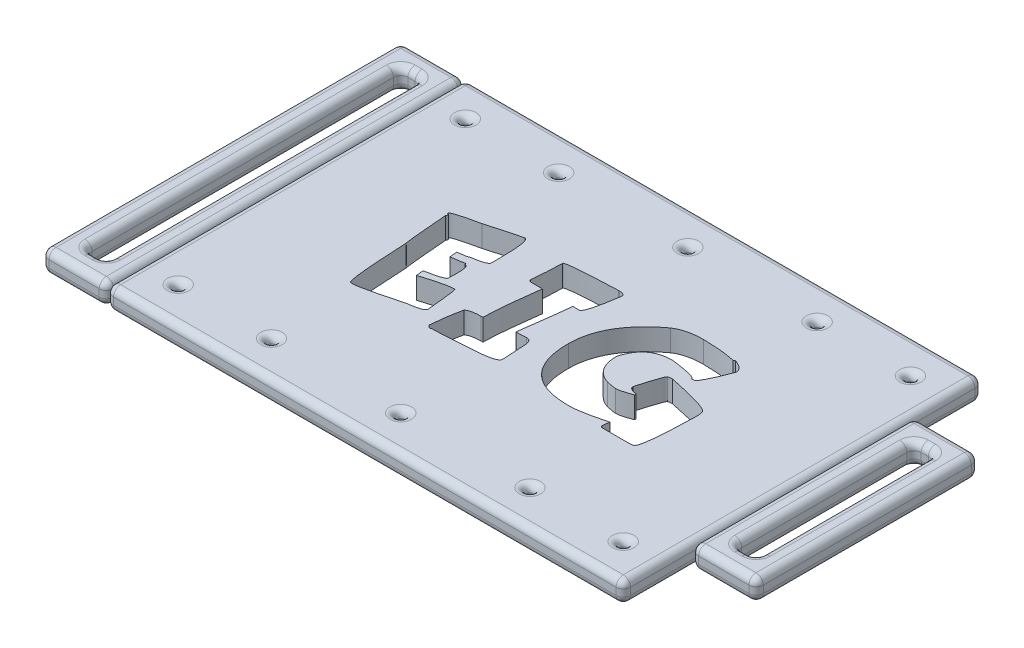
SolidWorks part; units mm, degrees
ref_plane "Front Plane" through (0, 0, 0) normal (0, 0, 1) x (1, 0, 0)
ref_plane "Top Plane" through (0, 0, 0) normal (0, 1, 0) x (1, 0, 0)
ref_plane "Right Plane" through (0, 0, 0) normal (1, 0, 0) x (0, 0, -1)
sketch "Sketch1" plane through (0, 0, 0) normal (0, 1, 0) x (1, 0, 0)
  line L1 (0, 0) -> (72, 0)
  line L2 (0, 0) -> (0, 50)
  line L3 (0, 50) -> (72, 50)
  line L4 (72, 0) -> (72, 50)
extrude "Boss-Extrude2" add sketch "Sketch1" along normal blind 3 contours L3 L4 L1 L2
sketch "Sketch8" plane through (0, 0, 0) normal (0, -1, 0) x (-1, 0, 0)
  line L0 (-72, 0) -> (-72, 50) construction
  line L1 (0, 0) -> (9, 0)
  line L2 (0, 0) -> (0, 50)
  line L3 (0, 50) -> (9, 50)
  line L4 (9, 0) -> (9, 50)
  line L5 (3, 47) -> (6, 47)
  line L6 (3, 47) -> (3, 3)
  line L7 (3, 3) -> (6, 3)
  line L8 (6, 47) -> (6, 3)
  line L17 (-72, 40.5) -> (-81, 40.5)
  line L18 (-72, 40.5) -> (-72, 9.5)
  line L19 (-72, 9.5) -> (-81, 9.5)
  line L20 (-81, 40.5) -> (-81, 9.5)
  line L21 (-78, 12.5) -> (-75, 12.5)
  line L22 (-78, 12.5) -> (-78, 37.5)
  line L23 (-78, 37.5) -> (-75, 37.5)
  line L24 (-75, 12.5) -> (-75, 37.5)
  dimension "D1" = 3
  dimension "D2" = 3
  dimension "D3" = 3
  dimension "D4" = 3
  dimension "D5" = 25
  dimension "D6" = 3
  dimension "D7" = 3
  dimension "D8" = 3
  dimension "D9" = 3
  dimension "D10" = 3
  dimension "D11" = 9.5
  dimension "D12" = 9.5
  dimension "D13" = 3
extrude "Boss-Extrude4" add sketch "Sketch8" against normal blind 3 separate body
sketch "Sketch11" plane through (0, 3, 0) normal (0, 1, 0) x (1, 0, 0)
  circle A0 centre (5, 45) radius 0.5
  circle A1 centre (18, 45) radius 0.5
  circle A2 centre (36, 45) radius 0.5
  circle A3 centre (54, 45) radius 0.5
  circle A4 centre (67, 45) radius 0.5
  circle A5 centre (5, 5) radius 0.5
  circle A6 centre (18, 5) radius 0.5
  circle A7 centre (36, 5) radius 0.5
  circle A8 centre (54, 5) radius 0.5
  circle A9 centre (67, 5) radius 0.5
extrude "Cut-Extrude10" cut sketch "Sketch11" against normal blind 3
fillet "Fillet1" radius 1 24 edges at (0, 1.5, -50) (-6, 1.5, -3) (-6, 1.5, -47) (-4.5, 0, -50) (0, 0, -25) (-6, 0, -25) (-4.5, 0, -47) (-4.5, 0, -3) (-3, 1.5, -47) (-3, 1.5, -3) (-3, 0, -25) (-9, 1.5, -50) (-9, 0, -25) (-9, 3, -25) (-4.5, 3, -50) (0, 3, -25) (-4.5, 3, -47) (-6, 3, -25) (-4.5, 3, -3) (-3, 3, -25) (-9, 1.5, 0) (-4.5, 3, 0) (0, 1.5, 0) (-4.5, 0, 0)
fillet "Fillet2" radius 1 32 edges at (72, 1.5, -50) (0, 1.5, -50) (0, 1.5, 0) (72, 1.5, 0) (36, 0, 0) (72, 0, -25) (36, 0, -50) (0, 0, -25) (5, 0, -44.5) (18, 0, -44.5) (36, 0, -44.5) (54, 0, -44.5) (67, 0, -44.5) (5, 0, -4.5) (18, 0, -4.5) (36, 0, -4.5) (54, 0, -4.5) (67, 0, -4.5) (36, 3, -50) (72, 3, -25) (36, 3, 0) (0, 3, -25) (5, 3, -44.5) (18, 3, -44.5) (36, 3, -44.5) (54, 3, -44.5) (67, 3, -44.5) (5, 3, -4.5) (18, 3, -4.5) (36, 3, -4.5) (54, 3, -4.5) (67, 3, -4.5)
fillet "Fillet3" radius 1 24 edges at (72, 0, -25) (76.5, 0, -37.5) (76.5, 0, -12.5) (72, 3, -25) (76.5, 3, -37.5) (76.5, 3, -12.5) (81, 3, -25) (81, 0, -25) (72, 1.5, -9.5) (76.5, 3, -9.5) (81, 1.5, -9.5) (76.5, 0, -9.5) (78, 1.5, -37.5) (78, 3, -25) (78, 1.5, -12.5) (78, 0, -25) (75, 1.5, -12.5) (75, 3, -25) (75, 1.5, -37.5) (75, 0, -25) (81, 1.5, -40.5) (76.5, 3, -40.5) (72, 1.5, -40.5) (76.5, 0, -40.5)
sketch "Sketch12" plane through (0, 3, 0) normal (0, 1, 0) x (1, 0, 0)
  text T0 "EIG" font "Otaku Rant" height in points 72
extrude "Cut-Extrude11" cut sketch "Sketch12" against normal blind 3
